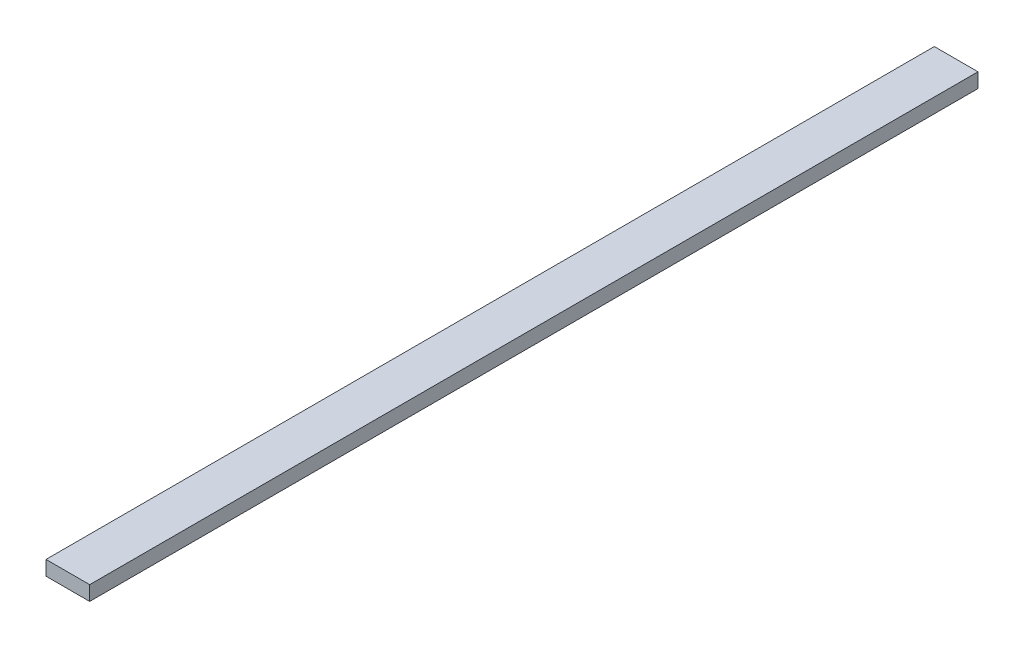
SolidWorks part; units mm, degrees
ref_plane "Front Plane" through (0, 0, 0) normal (0, 0, 1) x (1, 0, 0)
ref_plane "Top Plane" through (0, 0, 0) normal (0, 1, 0) x (1, 0, 0)
ref_plane "Right Plane" through (0, 0, 0) normal (1, 0, 0) x (0, 0, -1)
sketch "Esboço2" plane through (0, 0, 0) normal (0, 0, 1) x (1, 0, 0)
  line L12 (183, -8.5) -> (183, -3.5)
  line L13 (168, -3.5) -> (168, -8.5)
  line L14 (168, -8.5) -> (183, -8.5)
  line L15 (183, -3.5) -> (168, -3.5)
extrude "Ressalto-extrusão1" add sketch "Esboço2" along normal blind 305
